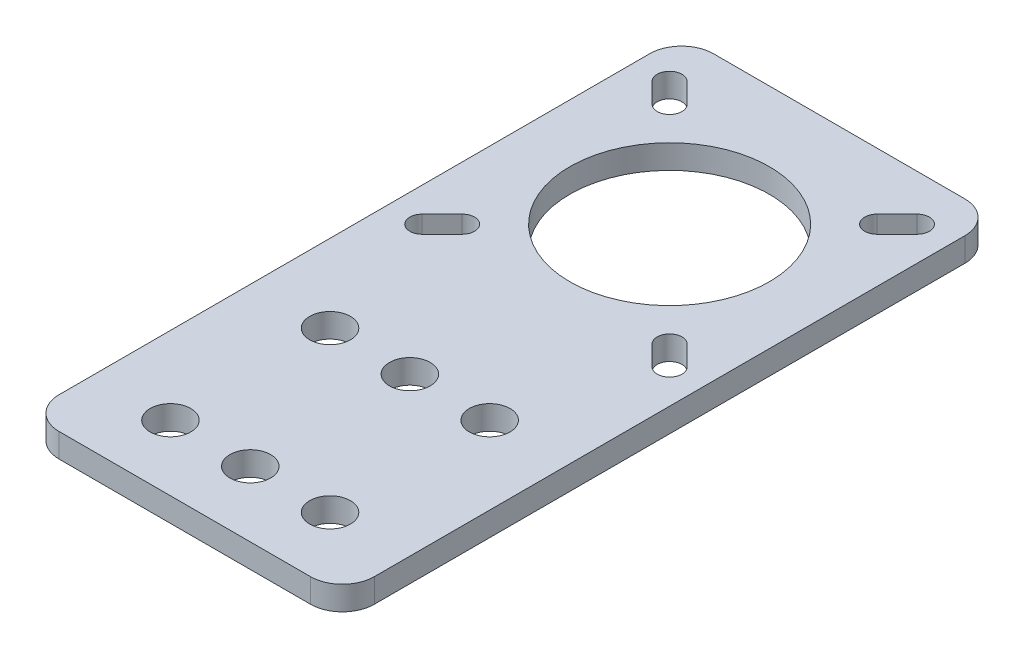
SolidWorks part; units mm, degrees
material "6061-T6 (SS)"
ref_plane "Front Plane" through (0, 0, 0) normal (0, 0, 1) x (1, 0, 0)
ref_plane "Top Plane" through (0, 0, 0) normal (0, 1, 0) x (1, 0, 0)
ref_plane "Right Plane" through (0, 0, 0) normal (1, 0, 0) x (0, 0, -1)
sketch "Sketch1" plane through (0, 0, 0) normal (0, 1, 0) x (1, 0, 0)
  line L0 (0, 0) -> (30, 0) construction
  line L1 (15.75, -60.75) -> (-15.75, -60.75)
  line L2 (19.75, -56.75) -> (19.75, 17.25)
  line L3 (15.75, 21.25) -> (-15.75, 21.25)
  line L4 (-19.75, -56.75) -> (-19.75, 17.25)
  line L5 (0, 21.25) -> (0, 0) construction
  line L6 (13, 13) -> (15.5, 15.5) construction
  line L7 (11.904, 14.096) -> (14.404, 16.596)
  line L8 (14.096, 11.904) -> (16.596, 14.404)
  line L9 (10, -52.55) -> (0, -52.55) construction
  line L10 (-13, 13) -> (-15.5, 15.5) construction
  line L11 (-11.904, 14.096) -> (-14.404, 16.596)
  line L12 (-14.096, 11.904) -> (-16.596, 14.404)
  line L13 (-13, -13) -> (-15.5, -15.5) construction
  line L14 (-11.904, -14.096) -> (-14.404, -16.596)
  line L15 (-14.096, -11.904) -> (-16.596, -14.404)
  line L16 (13, -13) -> (15.5, -15.5) construction
  line L17 (11.904, -14.096) -> (14.404, -16.596)
  line L18 (14.096, -11.904) -> (16.596, -14.404)
  line L22 (0, 0) -> (27.1737, 27.1737) construction
  arc A0 (-15.75, -60.75) -> (-19.75, -56.75) centre (-15.75, -56.75) cw
  arc A1 (15.75, -60.75) -> (19.75, -56.75) centre (15.75, -56.75) ccw
  arc A2 (19.75, 17.25) -> (15.75, 21.25) centre (15.75, 17.25) ccw
  arc A3 (-15.75, 21.25) -> (-19.75, 17.25) centre (-15.75, 17.25) ccw
  circle A4 centre (0, 0) radius 12.5
  arc A5 (11.904, 14.096) -> (14.096, 11.904) centre (13, 13) ccw
  arc A6 (16.596, 14.404) -> (14.404, 16.596) centre (15.5, 15.5) ccw
  circle A7 centre (10, -52.55) radius 2.55
  circle A8 centre (10, -32.55) radius 2.55
  circle A9 centre (0, -52.55) radius 2.55
  circle A10 centre (0, -32.55) radius 2.55
  circle A11 centre (-10, -52.55) radius 2.55
  circle A12 centre (-10, -32.55) radius 2.55
  arc A13 (-11.904, 14.096) -> (-14.096, 11.904) centre (-13, 13) cw
  arc A14 (-16.596, 14.404) -> (-14.404, 16.596) centre (-15.5, 15.5) cw
  arc A15 (-11.904, -14.096) -> (-14.096, -11.904) centre (-13, -13) ccw
  arc A16 (-16.596, -14.404) -> (-14.404, -16.596) centre (-15.5, -15.5) ccw
  arc A17 (11.904, -14.096) -> (14.096, -11.904) centre (13, -13) cw
  arc A18 (16.596, -14.404) -> (14.404, -16.596) centre (15.5, -15.5) cw
  point P4 (14.25, 14.25)
  point P40 (-14.25, 14.25)
  point P47 (-14.25, -14.25)
  point P54 (14.25, -14.25)
  dimension "D2" = 4
  dimension "D3" = 60.75
  dimension "D5" = 3.1
  dimension "D7" = 20
  dimension "D10" = 3
  dimension "D4" = 25
  dimension "D8" = 9.75
  dimension "D14" = 8.25
  dimension "D6" = 5.1
  dimension "D1" = 82
  dimension "D9" = 39.5
  dimension "D11" = 10
  dimension "D12" = 8.2
  dimension "D13" = 5.75
  dimension "D16" = 45
extrude "Boss-Extrude1" add sketch "Sketch1" along normal blind 3
